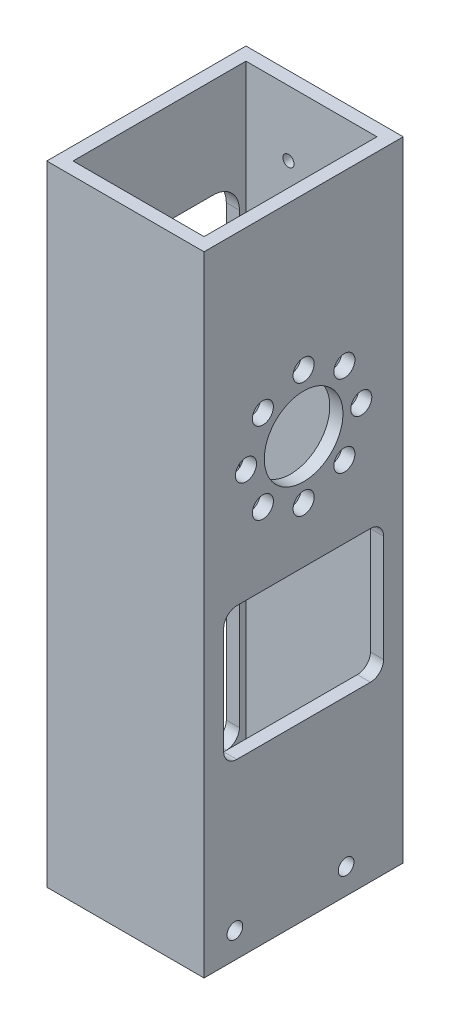
SolidWorks part; units mm, degrees
material "6061 Alloy"
ref_plane "Front" through (0, 0, 0) normal (0, 0, 1) x (1, 0, 0)
ref_plane "Top" through (0, 0, 0) normal (0, 1, 0) x (1, 0, 0)
ref_plane "Right" through (0, 0, 0) normal (1, 0, 0) x (0, 0, -1)
sketch "Sketch1" plane through (0, 0, 0) normal (0, 1, 0) x (1, 0, 0)
  line L1 (-19.05, -24.13) -> (19.05, -24.13)
  line L2 (-19.05, -24.13) -> (-19.05, 24.13)
  line L3 (-19.05, 24.13) -> (19.05, 24.13)
  line L4 (19.05, -24.13) -> (19.05, 24.13)
  line L5 (-19.05, -24.13) -> (19.05, 24.13) construction
  line L6 (-19.05, 24.13) -> (19.05, -24.13) construction
  line L10 (15.875, 20.955) -> (-15.875, 20.955)
  line L14 (15.875, 20.955) -> (15.875, -20.955)
  line L15 (15.875, -20.955) -> (-15.875, -20.955)
  line L16 (-15.875, -20.955) -> (-15.875, 20.955)
  point P0 (0, 0)
  dimension "D1" = 38.1
  dimension "D2" = 48.26
  dimension "D3" = 3.175
  dimension "D4" = 3.175
  dimension "D5" = 3.175
  dimension "D6" = 3.175
extrude "Boss-Extrude1" add sketch "Sketch1" along normal blind 152.4
sketch "Sketch2" plane through (-15.875, 0, 0) normal (1, 0, 0) x (0, 0, -1)
  circle A0 centre (-16.6454, 6.2154) radius 1.8986
  circle A1 centre (10.3003, 6.1824) radius 1.8986
  dimension "D1" = 3.7973
extrude "Cut-Extrude1" cut sketch "Sketch2" against normal through all both and the other way through all
sketch "Sketch4" plane through (-19.05, 0, 0) normal (-1, 0, 0) x (0, 0, 1)
  line L0 (-24.13, 152.4) -> (-24.13, 0) construction
  line L1 (16.1925, 10.16) -> (-16.1925, 10.16)
  line L2 (19.3675, 13.335) -> (19.3675, 64.135)
  line L3 (16.1925, 67.31) -> (-16.1925, 67.31)
  line L4 (-19.3675, 13.335) -> (-19.3675, 64.135)
  line L5 (19.3675, 10.16) -> (-19.3675, 67.31) construction
  line L6 (19.3675, 67.31) -> (-19.3675, 10.16) construction
  line L7 (24.13, 152.4) -> (24.13, 0) construction
  line L8 (-24.13, 0) -> (24.13, 0) construction
  arc A0 (-16.1925, 67.31) -> (-19.3675, 64.135) centre (-16.1925, 64.135) ccw
  arc A1 (19.3675, 64.135) -> (16.1925, 67.31) centre (16.1925, 64.135) ccw
  arc A2 (16.1925, 10.16) -> (19.3675, 13.335) centre (16.1925, 13.335) ccw
  arc A3 (-16.1925, 10.16) -> (-19.3675, 13.335) centre (-16.1925, 13.335) cw
  point P4 (0, 38.735)
  dimension "D4" = 3.175
  dimension "D1" = 4.7625
  dimension "D2" = 4.7625
  dimension "D3" = 10.16
  dimension "D5" = 57.15
extrude "Cut-Extrude3" cut sketch "Sketch4" against normal blind 3.175
sketch "Sketch5" plane through (19.05, 0, 0) normal (1, 0, 0) x (0, 0, -1)
  line L0 (24.13, 152.4) -> (24.13, 0) construction
  line L1 (16.1925, 67.31) -> (-16.1925, 67.31)
  line L2 (19.3675, 64.135) -> (19.3675, 45.085)
  line L3 (16.1925, 41.91) -> (-16.1925, 41.91)
  line L4 (-19.3675, 64.135) -> (-19.3675, 45.085)
  line L5 (19.3675, 67.31) -> (-19.3675, 41.91) construction
  line L6 (19.3675, 41.91) -> (-19.3675, 67.31) construction
  line L7 (-24.13, 152.4) -> (-24.13, 0) construction
  line L10 (24.13, 0) -> (-24.13, 0) construction
  arc A0 (-16.1925, 41.91) -> (-19.3675, 45.085) centre (-16.1925, 45.085) cw
  arc A1 (-16.1925, 67.31) -> (-19.3675, 64.135) centre (-16.1925, 64.135) ccw
  arc A2 (19.3675, 45.085) -> (16.1925, 41.91) centre (16.1925, 45.085) cw
  arc A3 (16.1925, 67.31) -> (19.3675, 64.135) centre (16.1925, 64.135) cw
  point P4 (0, 54.61)
  dimension "D5" = 3.175
  dimension "D1" = 4.7625
  dimension "D2" = 4.7625
  dimension "D3" = 67.31
  dimension "D4" = 25.4
extrude "Cut-Extrude4" cut sketch "Sketch5" against normal blind 3.175
sketch "Sketch6" plane through (-15.875, 0, 0) normal (1, 0, 0) x (0, 0, -1)
  line L0 (0, 101.6) -> (0, 0) construction
  line L1 (0, 87.63) -> (0, 101.6) construction
  circle A0 centre (0, 101.6) radius 9.525
  circle A1 centre (0, 87.63) radius 2.5527
  circle A2 centre (-9.8783, 91.7217) radius 2.5527
  circle A3 centre (-13.97, 101.6) radius 2.5527
  circle A4 centre (-9.8783, 111.4783) radius 2.5527
  circle A5 centre (0, 115.57) radius 2.5527
  circle A6 centre (9.8783, 111.4783) radius 2.5527
  circle A7 centre (13.97, 101.6) radius 2.5527
  circle A8 centre (9.8783, 91.7217) radius 2.5527
  point P22 (0, 101.6)
  dimension "D1" = 19.05
  dimension "D3" = 5.1054
  dimension "D2" = 101.6
  dimension "D4" = 13.97
  dimension "D6" = 0
  dimension "D5" = 8
extrude "Cut-Extrude5" cut sketch "Sketch6" along normal up to next
sketch "Sketch7" plane through (-19.05, 0, 0) normal (-1, 0, 0) x (0, 0, 1)
  line L0 (24.13, 152.4) -> (24.13, 0) construction
  line L1 (-13.0175, 77.47) -> (13.0175, 77.47)
  line L2 (-19.3675, 83.82) -> (-19.3675, 121.92)
  line L3 (-13.0175, 128.27) -> (13.0175, 128.27)
  line L4 (19.3675, 83.82) -> (19.3675, 121.92)
  line L5 (-19.3675, 77.47) -> (19.3675, 128.27) construction
  line L6 (-19.3675, 128.27) -> (19.3675, 77.47) construction
  line L7 (-24.13, 152.4) -> (-24.13, 0) construction
  line L8 (16.51, 67.31) -> (-16.51, 67.31) construction
  arc A0 (-19.3675, 121.92) -> (-13.0175, 128.27) centre (-13.0175, 121.92) cw
  arc A1 (13.0175, 128.27) -> (19.3675, 121.92) centre (13.0175, 121.92) cw
  arc A2 (13.0175, 77.47) -> (19.3675, 83.82) centre (13.0175, 83.82) ccw
  arc A3 (-13.0175, 77.47) -> (-19.3675, 83.82) centre (-13.0175, 83.82) cw
  point P4 (0, 102.87)
  dimension "D5" = 6.35
  dimension "D1" = 50.8
  dimension "D2" = 4.7625
  dimension "D3" = 4.7625
  dimension "D4" = 10.16
extrude "Cut-Extrude6" cut sketch "Sketch7" against normal blind 3.175
sketch "Sketch11" plane through (0, 0, -24.13) normal (0, 0, -1) x (-1, 0, 0)
  line L0 (-5.5796, 136.6393) -> (5.5796, 136.6393) construction
  line L1 (0, 136.6393) -> (0, 152.4) construction
  line L2 (-19.05, 152.4) -> (19.05, 152.4) construction
hole_wizard "#6-32 Tapped Hole2" positions "3DSketch2" profile "Sketch12" tap size "#6-32" standard "ANSI Inch" end condition up to next
sketch3d "3DSketch2"
  point P0 (5.5796, 136.6393, -24.13)
  point P3 (-5.5796, 136.6393, -24.13)
cosmetic thread "Hole Thread1" parameters "D2"=3.5052
cosmetic thread "Hole Thread2" parameters "D2"=3.5052
sketch "Sketch12" plane through (5.5796, 136.6393, -24.13) normal (1, 0, 0) x (0, 1, 0)
  line L0 (0, 0) -> (0, 3.175)
  line L1 (0, 3.175) -> (1.3525, 3.175)
  line L2 (1.3525, 3.175) -> (1.3525, 0)
  line L5 (1.3525, 0) -> (0, 0)
  line L11 (0, -6.35) -> (0, 107.95) construction
  dimension "Thru Tap Drill Dia." = 2.7051
  dimension "Thru Tap Drill Depth" = 3.175
sketch "Sketch13" plane through (19.05, 0, 0) normal (1, 0, 0) x (0, 0, -1)
  line L2 (0, 78.486) -> (19.3675, 78.486)
  line L3 (19.3675, 78.486) -> (19.3675, 64.135)
  line L4 (0, 78.486) -> (-19.3675, 78.486)
  line L5 (-19.3675, 78.486) -> (-19.3675, 64.135)
  line L6 (19.3675, 64.135) -> (-19.3675, 64.135)
extrude "Cut-Extrude7" cut sketch "Sketch13" against normal up to next and the other way through all contours L3 L6 L5 L4 L2
fillet "Fillet1" radius 3.175 1 edges at (17.4625, 78.486, -19.3675)
fillet "Fillet2" radius 3.175 1 edges at (17.4625, 78.486, 19.3675)
sketch "Sketch15" plane through (-19.05, 0, 0) normal (-1, 0, 0) x (0, 0, 1)
  line L0 (0, 67.31) -> (0, 78.486) construction
  line L1 (16.1925, 67.31) -> (-16.1925, 67.31) construction
  line L2 (0, 78.486) -> (0, 88.646) construction
  line L3 (0, 78.486) -> (-19.3675, 78.486)
  line L4 (0, 78.486) -> (19.3675, 78.486)
  line L5 (0, 88.646) -> (19.3675, 88.646)
  line L6 (19.3675, 83.82) -> (19.3675, 121.92) construction
  line L7 (19.3675, 88.646) -> (19.3675, 78.486)
  line L8 (0, 88.646) -> (-19.3675, 88.646)
  line L9 (-19.3675, 121.92) -> (-19.3675, 83.82) construction
  line L10 (-19.3675, 88.646) -> (-19.3675, 78.486)
  dimension "D1" = 11.176
  dimension "D2" = 10.16
extrude "Boss-Extrude2" add sketch "Sketch15" against normal blind 3.175
sketch "Sketch16" plane through (-19.05, 0, 0) normal (-1, 0, 0) x (0, 0, 1)
  line L0 (0, 78.486) -> (19.3675, 78.486)
  line L1 (-16.4629, 78.486) -> (16.4629, 78.486) construction
  line L2 (19.3675, 78.486) -> (19.3675, 64.135)
  line L3 (19.3675, 64.135) -> (-19.3675, 64.135)
  line L4 (-19.3675, 64.135) -> (-19.3675, 78.486)
  line L5 (-19.3675, 78.486) -> (0, 78.486)
extrude "Cut-Extrude8" cut sketch "Sketch16" against normal up to next
fillet "Fillet3" radius 3.175 1 edges at (-17.4625, 78.486, 19.3675)
fillet "Fillet4" radius 3.175 1 edges at (-17.4625, 78.486, -19.3675)
fillet "Fillet5" radius 6.35 1 edges at (-17.4625, 88.646, -19.3675)
fillet "Fillet6" radius 6.35 1 edges at (-17.4625, 88.646, 19.3675)
sketch "Sketch17" plane through (-19.05, 0, 0) normal (-1, 0, 0) x (0, 0, 1)
  line L0 (0, 78.486) -> (0, 74.168) construction
  line L1 (-16.1925, 78.486) -> (16.1925, 78.486) construction
  line L2 (0, 74.168) -> (19.3675, 74.168)
  line L3 (19.3675, 13.335) -> (19.3675, 75.311) construction
  line L4 (19.3675, 74.168) -> (19.3675, 84.3547)
  line L5 (19.3675, 84.3547) -> (-20.6375, 84.3547)
  line L6 (-20.6375, 84.3547) -> (-19.3675, 74.168)
  line L7 (-19.3675, 75.311) -> (-19.3675, 13.335) construction
  line L8 (-19.3675, 74.168) -> (0, 74.168)
  dimension "D1" = 4.318
extrude "Boss-Extrude3" add sketch "Sketch17" against normal blind 3.175
sketch "Sketch18" plane through (-19.05, 0, 0) normal (-1, 0, 0) x (0, 0, 1)
  line L0 (0, 74.168) -> (0, 84.328) construction
  line L1 (-19.3675, 74.168) -> (19.3675, 74.168) construction
  line L2 (0, 84.328) -> (-19.3675, 84.328)
  line L3 (-19.3675, 84.328) -> (-19.3675, 94.996)
  line L4 (-19.3675, 94.996) -> (19.3675, 94.996)
  line L5 (19.3675, 94.996) -> (19.3675, 84.328)
  line L6 (19.3675, 84.328) -> (0, 84.328)
  dimension "D1" = 10.16
extrude "Cut-Extrude9" cut sketch "Sketch18" against normal up to next
sketch "Sketch19" plane through (19.05, 0, 0) normal (1, 0, 0) x (0, 0, -1)
  line L0 (0, 78.486) -> (0, 74.168) construction
  line L1 (16.1925, 78.486) -> (-16.1925, 78.486) construction
  line L2 (0, 74.168) -> (19.3675, 74.168)
  line L3 (19.3675, 45.085) -> (19.3675, 75.311) construction
  line L4 (19.3675, 74.168) -> (19.3675, 78.486)
  line L5 (19.3675, 78.486) -> (-19.3675, 78.486)
  line L6 (0, 74.168) -> (-19.3675, 74.168)
  line L7 (-19.3675, 75.311) -> (-19.3675, 45.085) construction
  line L8 (-19.3675, 74.168) -> (-19.3675, 78.486)
  dimension "D1" = 4.318
extrude "Boss-Extrude4" add sketch "Sketch19" against normal blind 3.175
fillet "Fillet7" radius 3.175 1 edges at (17.4625, 74.168, -19.3675)
fillet "Fillet8" radius 3.175 1 edges at (17.4625, 74.168, 19.3675)
fillet "Fillet9" radius 3.175 1 edges at (-17.4625, 74.168, 19.3675)
fillet "Fillet10" radius 3.175 1 edges at (-17.4625, 74.168, -19.3675)
fillet "Fillet11" radius 6.35 1 edges at (-17.4625, 84.328, -19.3675)
fillet "Fillet12" radius 6.35 1 edges at (-17.4625, 84.328, 19.3675)
